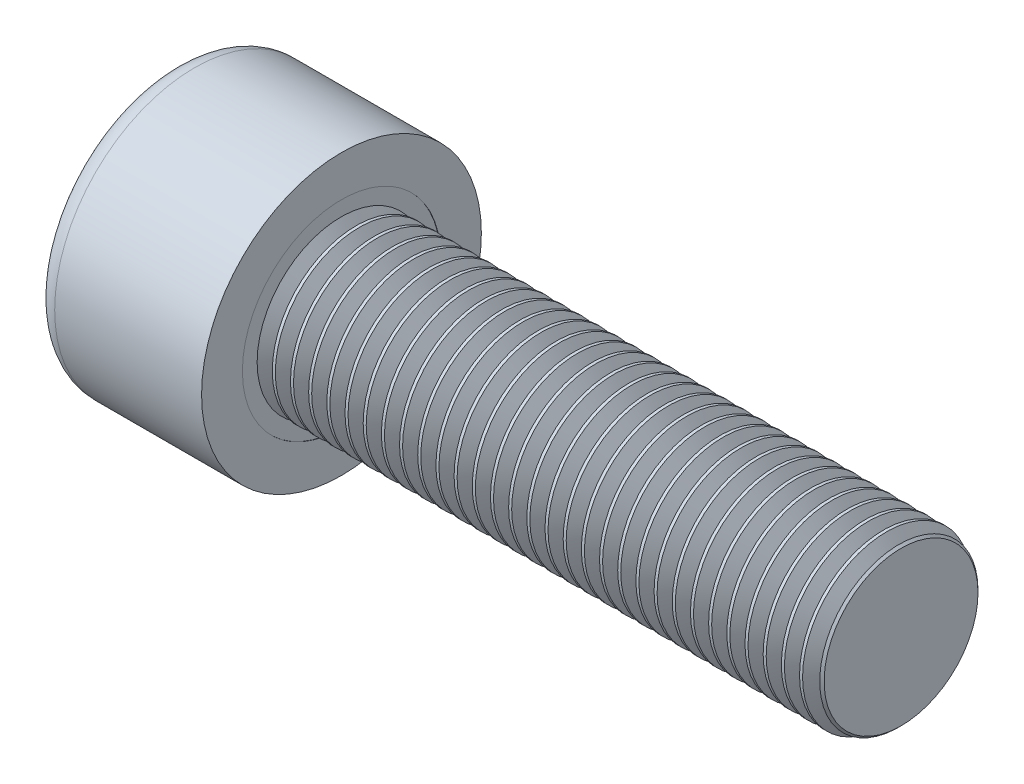
SolidWorks part; units mm, degrees
ref_plane "Front" through (0, 0, 0) normal (0, 0, 1) x (1, 0, 0)
ref_plane "Top" through (0, 0, 0) normal (0, 1, 0) x (1, 0, 0)
ref_plane "Right" through (0, 0, 0) normal (1, 0, 0) x (0, 0, -1)
sketch "Sketch1" plane through (0, 0, 0) normal (1, 0, 0) x (0, 0, -1)
  circle A0 centre (0, 0) radius 5
  dimension "dk" = 10
extrude "BaseHead" add sketch "Sketch1" along normal blind 6
sketch "Sketch2" plane through (6, 0, 0) normal (1, 0, 0) x (0, 0, -1)
  circle A0 centre (0, 0) radius 3
  dimension "d" = 6
extrude "BaseBody" add sketch "Sketch2" along normal blind 20
cosmetic thread "ThreadCosmetic1" [suppressed] parameters "b"=20, "D2"=4.917
sketch "Sketch3" plane through (0, 0, 0) normal (1, 0, 0) x (0, 0, -1)
  line L1 (2.8868, 0) -> (1.4434, 2.5)
  line L2 (1.4434, 2.5) -> (-1.4434, 2.5)
  line L3 (-1.4434, 2.5) -> (-2.8868, 0)
  line L4 (-2.8868, 0) -> (-1.4434, -2.5)
  line L5 (-1.4434, -2.5) -> (1.4434, -2.5)
  line L6 (1.4434, -2.5) -> (2.8868, 0)
  circle A0 centre (0, 0) radius 2.5 construction
  dimension "s" = 5
  dimension "e" = 5.7735
extrude "HexagonSocket" cut sketch "Sketch3" along normal blind 3
sketch "Sketch4" plane through (-4.1961, 0.75, 0) normal (0, 0, 1) x (-1, 0, 0)
  line L0 (-7.1961, 3.25) -> (-8.6395, 0.75)
  line L2 (-8.6395, 0.75) -> (-7.1961, 0.75)
  line L3 (-7.1961, 0.75) -> (-7.1961, 3.25)
  line L4 (-5.0351, 0.75) -> (0.839, 0.75) construction
  line L5 (-30.1961, 0.75) -> (-10.1961, 0.75) construction
  line L6 (-10.1961, 0.75) -> (-4.1961, 0.75) construction
  dimension "m" = 60
revolve "Cut-Revolve1" cut sketch "Sketch4" angle 360 about L4
fillet "HeadFillet" [suppressed] radius 0.25
fillet "TopFillet" radius 0.75 1 edges at (0, 0, -5)
chamfer "Chamfer1" distance 0.25 angle 45 1 edges at (26, 0, -3)
sketch "Sketch5" plane through (0, 0, 0) normal (0, 0, 1) x (1, 0, 0)
  line L0 (25.75, 2.531) -> (26.0208, 3)
  line L1 (26.0208, 3) -> (26.0208, 3.5415)
  line L2 (26.0208, 3.5415) -> (25.4793, 3.5415)
  line L3 (25.4793, 3.5415) -> (25.4793, 3)
  line L4 (25.4793, 3) -> (25.75, 2.531)
  line L5 (0, 0) -> (7.8886, 0) construction
  line L6 (25.75, -3) -> (25.75, 3) construction
  dimension "D1" = 6
  dimension "D2" = 0.5415
revolve "Cut-Revolve10" cut sketch "Sketch5" angle 360 about L5
pattern_linear "LPattern10" count 31 spacing 0.6498 along (-1, 0, 0) of "Cut-Revolve10"
equation "\"r1@TopFillet\" = \"d@Sketch2\" / 8"
equation "\"D1@Chamfer1\" = \"r@HeadFillet\""
equation "\"D1@Sketch5\" = \"d@Sketch2\""
equation "\"D2@Sketch5\" =  ( \"d@Sketch2\" - \"D2@ThreadCosmetic1\" )  / 2"
equation "\"D3@LPattern10\" = \"D2@Sketch5\" * 1.2"
equation "\"D1@LPattern10\" = \"b@ThreadCosmetic1\" / \"D3@LPattern10\""
